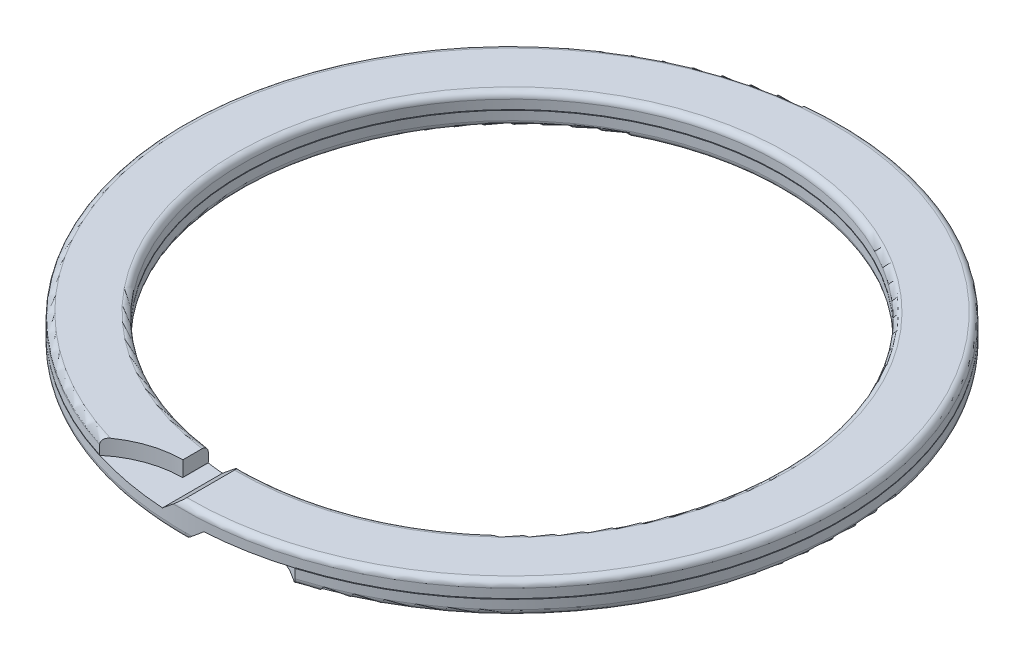
SolidWorks part; units mm, degrees
material "1070"
ref_plane "Front Plane" through (0, 0, 0) normal (0, 0, 1) x (1, 0, 0)
ref_plane "Top Plane" through (0, 0, 0) normal (0, 1, 0) x (1, 0, 0)
ref_plane "Right Plane" through (0, 0, 0) normal (1, 0, 0) x (0, 0, -1)
sketch "Sketch1" plane through (0, 0, 0) normal (1, 0, 0) x (0, 0, -1)
  line L0 (8.788, -0.495) -> (10.302, -0.495)
  line L1 (10.5, -0.297) -> (10.5, 0.297)
  line L2 (10.302, 0.495) -> (8.788, 0.495)
  line L3 (8.59, 0.297) -> (8.59, -0.297)
  line L4 (0, -1) -> (0, 1) construction
  arc A0 (8.59, -0.297) -> (8.788, -0.495) centre (8.788, -0.297) ccw
  arc A1 (10.302, -0.495) -> (10.5, -0.297) centre (10.302, -0.297) ccw
  arc A2 (10.5, 0.297) -> (10.302, 0.495) centre (10.302, 0.297) ccw
  arc A3 (8.788, 0.495) -> (8.59, 0.297) centre (8.788, 0.297) ccw
revolve "Revolve1" add sketch "Sketch1" angle 360 about L4
sketch "Sketch2" plane through (0, 0, 0) normal (0, 1, 0) x (1, 0, 0)
  line L0 (-1.1657, -15.3692) -> (-1.1657, -9.3208)
  arc A0 (-1.1657, -9.3208) -> (-1.1657, -15.3692) centre (-1.1657, -12.345) ccw
extrude "Cut-Extrude1" cut sketch "Sketch2" along normal blind 21
sketch "Sketch3" plane through (0, 0, 0) normal (0, 1, 0) x (1, 0, 0)
  line L0 (1.1657, -9.3208) -> (1.1657, -15.3692)
  arc A0 (1.1657, -15.3692) -> (1.1657, -9.3208) centre (1.1657, -12.345) ccw
extrude "Cut-Extrude2" cut sketch "Sketch3" against normal blind 21
sketch "Sketch4" plane through (0, 0, 0) normal (0, 0, 1) x (1, 0, 0)
  line L0 (-1.1667, 1.0885) -> (-1.1667, 0)
  line L1 (-1.1667, 0) -> (-0.6594, 0)
  line L2 (-0.6594, 0) -> (0.66, 1.0885)
  line L3 (0.66, 1.0885) -> (-1.1667, 1.0885)
extrude "Cut-Extrude3" cut sketch "Sketch4" along normal blind 21
sketch "Sketch5" plane through (0, 0, 0) normal (0, 0, 1) x (1, 0, 0)
  line L0 (-0.66, -1.0885) -> (1.1667, -1.0885)
  line L1 (1.1667, -1.0885) -> (1.1667, 0)
  line L2 (1.1667, 0) -> (0.6594, 0)
  line L3 (0.6594, 0) -> (-0.66, -1.0885)
extrude "Cut-Extrude4" cut sketch "Sketch5" along normal blind 21
sketch "Sketch6" plane through (0, 0, 0) normal (0, 1, 0) x (1, 0, 0)
  line L0 (-10.71, -10.71) -> (-3.7108, -10.71)
  line L1 (-1.1657, -9.3208) -> (-1.1657, -8.5004)
  line L2 (1.1657, -8.5004) -> (1.1657, -9.3208)
  line L3 (3.7108, -10.71) -> (10.71, -10.71)
  line L4 (10.71, -10.71) -> (10.71, 10.71)
  line L5 (10.71, 10.71) -> (-10.71, 10.71)
  line L6 (-10.71, 10.71) -> (-10.71, -10.71)
  arc A0 (-3.7108, -10.71) -> (-1.1657, -9.3208) centre (-1.1667, -12.345) cw
  arc A1 (-1.1657, -8.5004) -> (1.1657, -8.5004) centre (0, 0) ccw
  arc A2 (1.1657, -9.3208) -> (3.7108, -10.71) centre (1.1667, -12.345) cw
extrude "Cut-Extrude5" cut sketch "Sketch6" along normal blind 0.01 and the other way blind 0.01
other "Freeze***"
